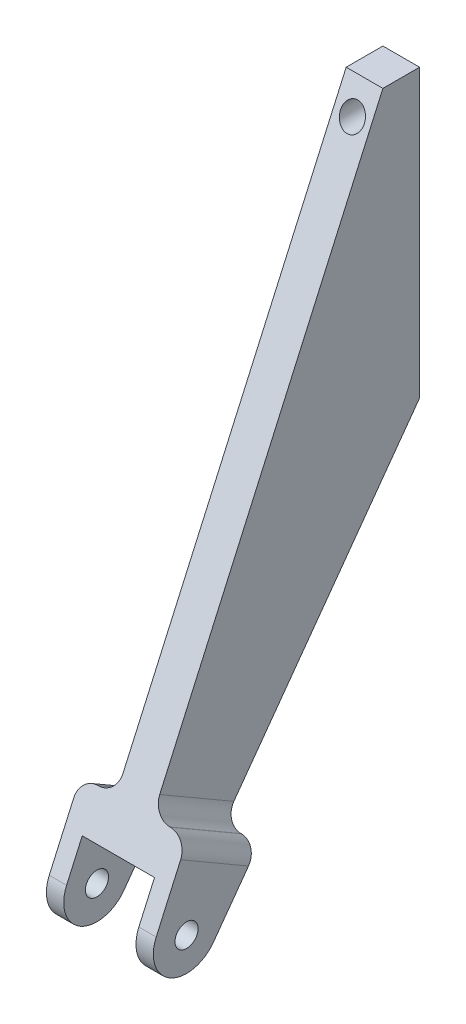
SolidWorks part; units mm, degrees
ref_plane "Front Plane" through (0, 0, 0) normal (0, 0, 1) x (1, 0, 0)
ref_plane "Top Plane" through (0, 0, 0) normal (0, 1, 0) x (1, 0, 0)
ref_plane "Right Plane" through (0, 0, 0) normal (1, 0, 0) x (0, 0, -1)
sketch "Sketch1" plane through (0, 0, 0) normal (0, 0, 1) x (1, 0, 0)
  line L1 (-72.0584, -12.4142) -> (-72.0584, -329.7013) construction
  line L2 (-72.0584, -9.0147) -> (-72.0584, -15.8137) construction
  line L3 (-54.5, -2.8892) -> (-105.0726, -2.8892) construction
  line L4 (-78.4084, -322.2124) -> (-65.7084, -322.2124)
  line L5 (-78.4084, -322.2124) -> (-78.4084, -2.8892)
  line L6 (-78.4084, -2.8892) -> (-65.7084, -2.8892)
  line L7 (-65.7084, -322.2124) -> (-65.7084, -2.8892)
  line L8 (-78.4084, -322.2124) -> (-65.7084, -2.8892) construction
  line L9 (-78.4084, -2.8892) -> (-65.7084, -322.2124) construction
  point P0 (-72.0584, -162.5508)
  dimension "D1" = 12.7
extrude "Boss-Extrude1" add sketch "Sketch1" along normal blind 112.776
sketch "Sketch2" plane through (-65.7084, 0, 0) normal (1, 0, 0) x (0, 0, -1)
  line L0 (0, -102) -> (-83.4596, -217.2296)
  line L1 (0, -322.2124) -> (0, -2.8892) construction
  line L2 (0, -2.8892) -> (-12.7, -2.8892)
  line L3 (-112.776, -2.8892) -> (0, -2.8892) construction
  line L4 (19.05, -102) -> (0, -102) construction
  line L5 (-12.7, -2.8892) -> (-103.2746, -205.7962)
  line L6 (0, -102) -> (0, -2.8892)
  line L8 (-143.9151, -343.6077) -> (30.3223, -343.6077)
  line L9 (-143.9151, -343.6077) -> (-143.9151, 9.7561)
  line L10 (-143.9151, 9.7561) -> (30.3223, 9.7561)
  line L11 (30.3223, -343.6077) -> (30.3223, 9.7561)
  circle A0 centre (9.525, -112) radius 142 construction
  circle A5 centre (9.525, -112) radius 142 construction
  arc A6 (-103.2746, -205.7962) -> (-83.4596, -217.2296) centre (-92.7733, -210.4838) ccw
  circle A7 centre (-92.7733, -210.4838) radius 4
  dimension "D4" = 23
  dimension "D5" = 8
  dimension "D1" = 12.7
extrude "Cut-Extrude1" cut sketch "Sketch2" against normal through all
sketch "Sketch3" plane through (0, 0, 0) normal (0, 0, -1) x (-1, 0, 0)
  line L0 (72, -12.4142) -> (72, -91.7892) construction
  circle A0 centre (72, -12.4142) radius 4.1275
  circle A1 centre (72, -91.7892) radius 4.1275
  dimension "D1" = 79.375
  dimension "D2" = 8.255
extrude "Cut-Extrude2" cut sketch "Sketch3" against normal blind 25.4
ref_plane "Plane1" through (-72.0584, 0, 0) normal (1, 0, 0) x (0, 0, -1)
sketch "Sketch4" plane through (-72.0584, 0, 0) normal (1, 0, 0) x (0, 0, -1)
  line L0 (-103.2746, -205.7962) -> (-92.3667, -181.3601)
  line L1 (-12.7, -2.8892) -> (-103.2746, -205.7962) construction
  line L2 (-92.3667, -181.3601) -> (-67.7963, -195.6038)
  line L3 (0, -102) -> (-83.4596, -217.2296) construction
  line L4 (-67.7963, -195.6038) -> (-83.4596, -217.2296)
  line L5 (-92.7733, -210.4838) -> (-23.7403, -91.4027) construction
  line L6 (0, -102) -> (-47.4806, -80.8054) construction
  circle A0 centre (-92.7733, -210.4838) radius 4
  arc A1 (-103.2746, -205.7962) -> (-83.4596, -217.2296) centre (-92.7733, -210.4838) ccw
  point P17 (0, 0)
  point P18 (-23.7403, -91.4027)
  dimension "D1" = 25.4
extrude "Boss-Extrude2" add sketch "Sketch4" along normal mid plane 37
sketch "Sketch6" plane through (-72.0584, 0, 0) normal (1, 0, 0) x (0, 0, -1)
  line L0 (-112.7681, -185.0219) -> (-58.6434, -216.3988)
  line L1 (-58.6434, -216.3988) -> (-86.651, -272.3911)
  line L2 (-86.651, -272.3911) -> (-155.3986, -233.0398)
  line L3 (-155.3986, -233.0398) -> (-112.7681, -185.0219)
  line L4 (-92.3667, -181.3601) -> (-67.7963, -195.6038) construction
  dimension "D1" = 12
extrude "Cut-Extrude3" cut sketch "Sketch6" against normal mid plane 25
fillet "Fillet1" radius 6 2 edges at (-78.4084, -188.482, 80.0815) (-65.7084, -188.482, 80.0815)
fillet "Fillet2" radius 6 2 edges at (-90.5584, -188.482, 80.0815) (-53.5584, -188.482, 80.0815)
